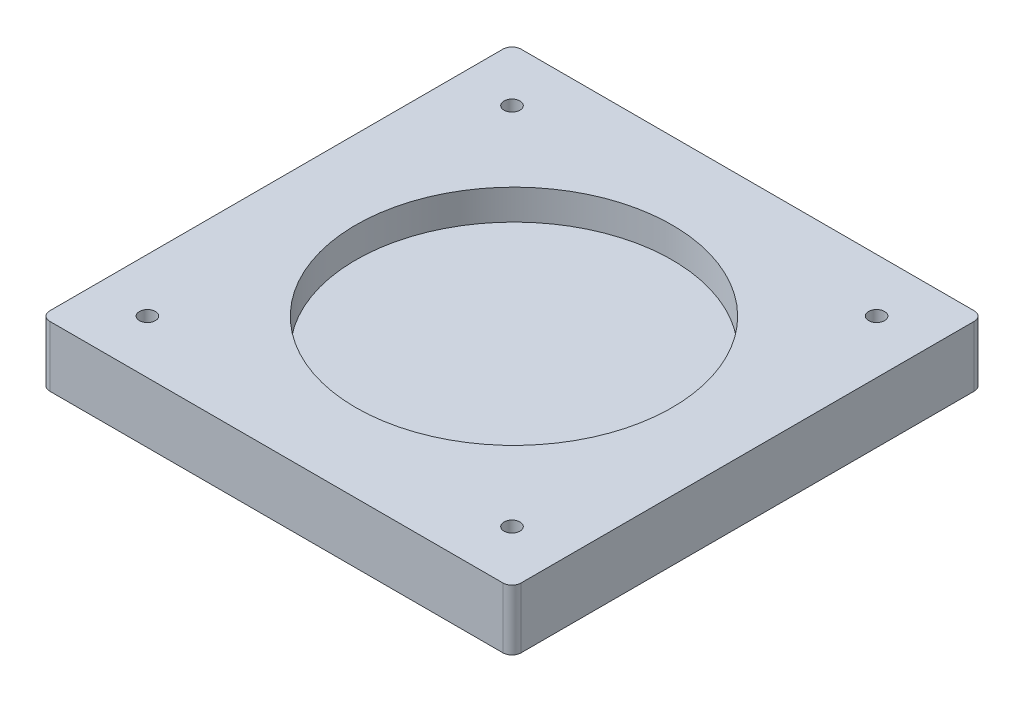
SolidWorks part; units mm, degrees
ref_plane "Front Plane" through (0, 0, 0) normal (0, 0, 1) x (1, 0, 0)
ref_plane "Top Plane" through (0, 0, 0) normal (0, 1, 0) x (1, 0, 0)
ref_plane "Right Plane" through (0, 0, 0) normal (1, 0, 0) x (0, 0, -1)
sketch "Sketch1" plane through (0, 0, 0) normal (0, 1, 0) x (1, 0, 0)
  line L0 (77.4608, -75.0982) -> (77.4608, 74.5774)
  line L1 (74.4472, 77.591) -> (-75.2284, 77.591)
  line L2 (-78.242, 74.5774) -> (-78.242, -75.0982)
  line L3 (-75.2284, -78.1118) -> (74.4472, -78.1118)
  circle A0 centre (-60.6043, -60.4741) radius 2.6376
  circle A1 centre (-60.6043, 59.9534) radius 2.6376
  circle A2 centre (59.8232, 59.9534) radius 2.6376
  circle A3 centre (59.8232, -60.4741) radius 2.6376
  arc A4 (77.4608, 74.5774) -> (74.4472, 77.591) centre (74.4472, 74.5774) ccw
  arc A5 (-75.2284, 77.591) -> (-78.242, 74.5774) centre (-75.2284, 74.5774) ccw
  arc A6 (-78.242, -75.0982) -> (-75.2284, -78.1118) centre (-75.2284, -75.0982) ccw
  arc A7 (74.4472, -78.1118) -> (77.4608, -75.0982) centre (74.4472, -75.0982) ccw
  circle A8 centre (0, 0) radius 73
  dimension "D2" = 146
  dimension "D1" = 155.7028
extrude "Boss-Extrude1" add sketch "Sketch1" along normal blind 20
sketch "Sketch4" plane through (0, 20, 0) normal (0, 1, 0) x (1, 0, 0)
  circle A2 centre (0, 0) radius 52.25
  circle A3 centre (0, 0) radius 73 construction
  circle A4 centre (0, 0) radius 73
extrude "Boss-Extrude2" add sketch "Sketch4" against normal blind 10
sketch "Sketch5" plane through (0, 10, 0) normal (0, -1, 0) x (1, 0, 0)
  circle A1 centre (0, 0) radius 73
  circle A2 centre (0, 0) radius 73
  dimension "D1" = 0
extrude "Boss-Extrude3" add sketch "Sketch5" along normal up to surface (10 mm away) up to face at (-0.3906, 0, 0.2604)
